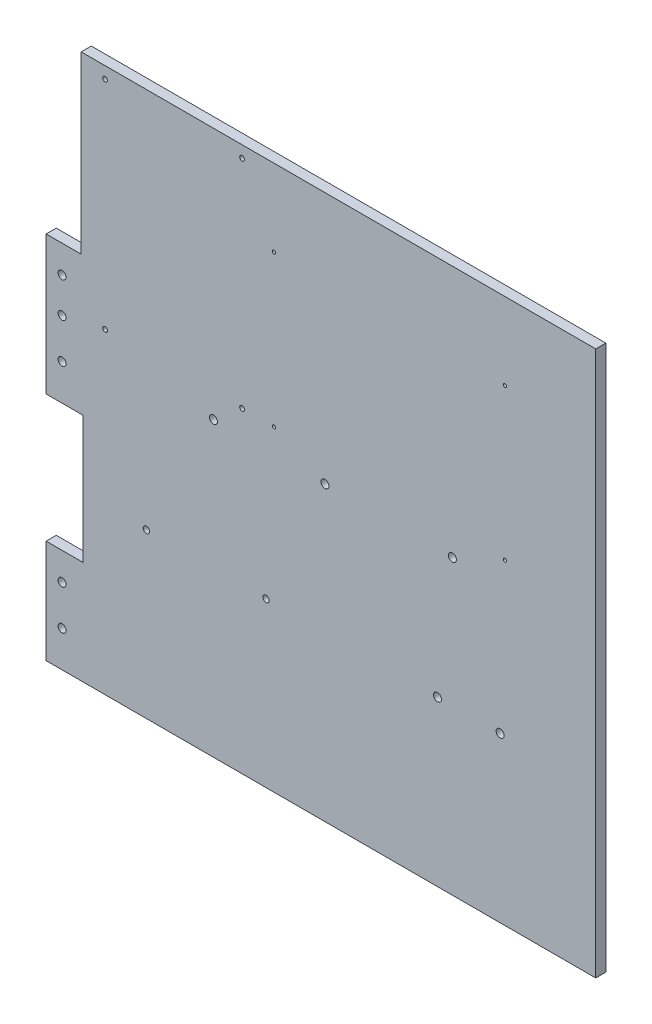
SolidWorks part; units mm, degrees
ref_plane "Front Plane" through (0, 0, 0) normal (0, 0, 1) x (1, 0, 0)
ref_plane "Top Plane" through (0, 0, 0) normal (0, 1, 0) x (1, 0, 0)
ref_plane "Right Plane" through (0, 0, 0) normal (1, 0, 0) x (0, 0, -1)
sketch "Model" plane through (0, 0, 0) normal (0, 0, 1) x (1, 0, 0)
  line L0 (731.3204, 258.0659) -> (386.3204, 258.0659)
  line L1 (731.3204, 258.0659) -> (731.3204, 600.0659)
  line L2 (731.3204, 600.0659) -> (408.3204, 600.0659)
  line L3 (408.3204, 600.0659) -> (408.3204, 490.0659)
  line L4 (408.3204, 490.0659) -> (386.3204, 490.0659)
  line L5 (409.3204, 403.0659) -> (409.3204, 323.0659)
  line L6 (386.3204, 258.0659) -> (386.3204, 323.0659)
  line L7 (386.3204, 323.0659) -> (409.3204, 323.0659)
  line L8 (409.3204, 403.0659) -> (386.3204, 403.0659)
  line L9 (386.3204, 403.0659) -> (386.3204, 490.0659)
  circle A0 centre (396.3204, 472.6874) radius 2.5
  circle A1 centre (396.3204, 450.6874) radius 2.5
  circle A2 centre (396.3204, 425.6874) radius 2.5
  circle A3 centre (396.3204, 305.6874) radius 2.5
  circle A4 centre (396.3204, 280.6874) radius 2.5
  circle A5 centre (491.3204, 441.6874) radius 2.5
  circle A6 centre (561.3204, 441.6874) radius 2.5
  circle A7 centre (641.3204, 441.6874) radius 2.5
  circle A8 centre (449.269, 360.6874) radius 2
  circle A9 centre (524.3204, 360.6874) radius 2
  circle A10 centre (423.3204, 592.6874) radius 1.5
  circle A11 centre (509.3204, 592.6874) radius 1.5
  circle A12 centre (509.3204, 456.6874) radius 1.5
  circle A13 centre (423.3204, 456.6874) radius 1.5
  circle A14 centre (529.3204, 551.6874) radius 1.05
  circle A15 centre (674.3204, 551.6874) radius 1.05
  circle A16 centre (529.3204, 456.6874) radius 1.05
  circle A17 centre (674.3204, 456.6874) radius 1.05
  circle A18 centre (631.9704, 361.0726) radius 2.5
  circle A19 centre (671.3204, 361.0726) radius 2.5
  point P50 (0, 0)
extrude "Boss-Extrude1" add sketch "Model" against normal blind 6.35
